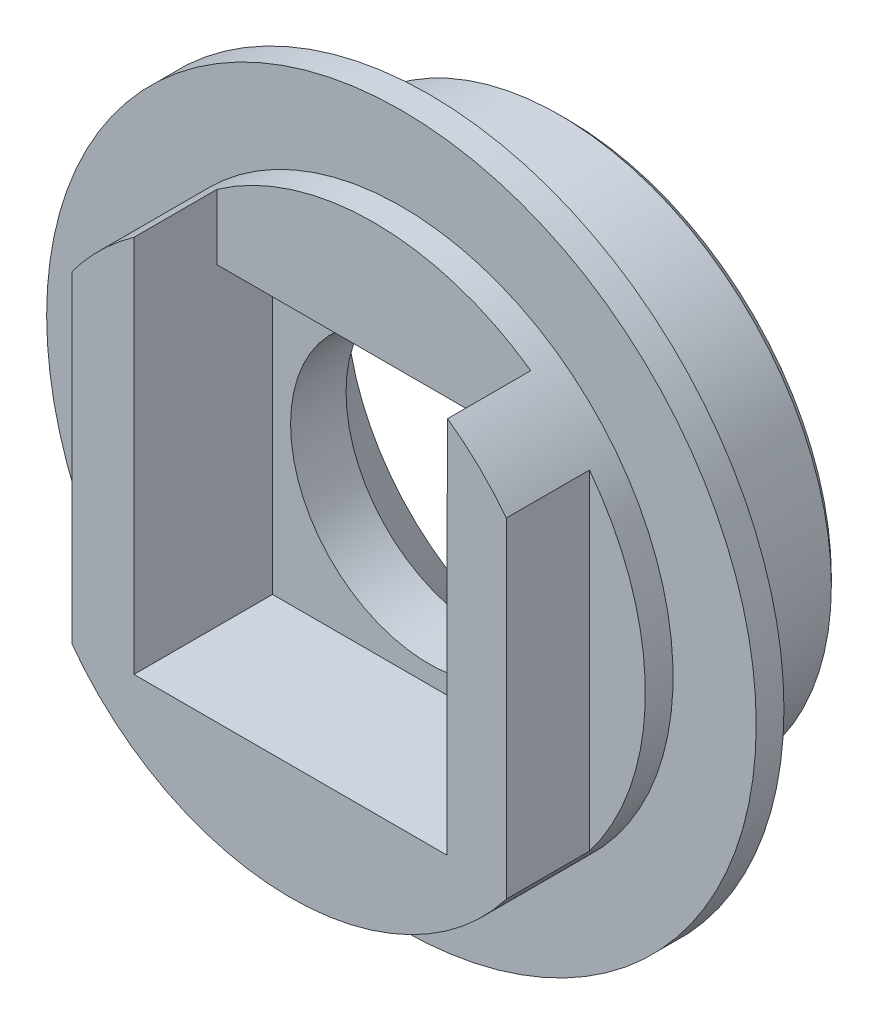
SolidWorks part; units mm, degrees
ref_plane "Front Plane" through (0, 0, 0) normal (0, 0, 1) x (1, 0, 0)
ref_plane "Top Plane" through (0, 0, 0) normal (0, 1, 0) x (1, 0, 0)
ref_plane "Right Plane" through (0, 0, 0) normal (1, 0, 0) x (0, 0, -1)
sketch "Sketch1" plane through (0, 0, 0) normal (0, 0, 1) x (1, 0, 0)
  circle A0 centre (0, 0) radius 9.8
  circle A1 centre (0, 0) radius 5
  dimension "D1" = 19.6
  dimension "D2" = 10
extrude "Boss-Extrude1" add sketch "Sketch1" along normal blind 10
sketch "Sketch2" plane through (0, 0, 10) normal (0, 0, 1) x (1, 0, 0)
  line L1 (-5.65, 5.65) -> (5.65, 5.65)
  line L2 (-5.65, 5.65) -> (-5.65, -5.65)
  line L3 (-5.65, -5.65) -> (5.65, -5.65)
  line L4 (5.65, 5.65) -> (5.65, -5.65)
  point P4 (5.65, 0)
  point P5 (0, 5.65)
  dimension "D1" = 11.3
  dimension "D2" = 11.3
extrude "Cut-Extrude1" cut sketch "Sketch2" against normal blind 5
sketch "Sketch3" plane through (0, 0, 10) normal (0, 0, 1) x (1, 0, 0)
  line L1 (-5.65, 5.65) -> (5.6634, 5.65)
  line L2 (-5.65, 5.65) -> (-5.65, 10.3571)
  line L3 (-5.65, 10.3571) -> (5.6634, 10.3571)
  line L4 (5.6634, 5.65) -> (5.6634, 10.3571)
extrude "Cut-Extrude2" cut sketch "Sketch3" against normal blind 3
sketch "Sketch4" plane through (0, 0, 10) normal (0, 0, 1) x (1, 0, 0)
  line L1 (-13.2922, 9.0382) -> (-7.8874, 9.0382)
  line L2 (-13.2922, 9.0382) -> (-13.2922, -9.0382)
  line L3 (-13.2922, -9.0382) -> (-7.8874, -9.0382)
  line L4 (-7.8874, 9.0382) -> (-7.8874, -9.0382)
  line L5 (13.4474, 9.0382) -> (7.784, 9.0382)
  line L6 (13.4474, 9.0382) -> (13.4474, -8.9089)
  line L7 (13.4474, -8.9089) -> (7.784, -8.9089)
  line L8 (7.784, 9.0382) -> (7.784, -8.9089)
extrude "Cut-Extrude3" cut sketch "Sketch4" against normal blind 3
chamfer "Chamfer1" distance 3 angle 45 1 edges at (5, 0, 0)
chamfer "Chamfer2" distance 0.29 angle 45 1 edges at (9.8, 0, 0)
ref_plane "Plane1" through (0, 0, 5) normal (0, 0, -1) x (-1, 0, 0)
sketch "Sketch5" plane through (0, 0, 5) normal (0, 0, -1) x (-1, 0, 0)
  circle A0 centre (0, 0) radius 9.8
  circle A1 centre (0, 0) radius 12.8
  dimension "D1" = 3
extrude "Boss-Extrude2" add sketch "Sketch5" against normal blind 1
